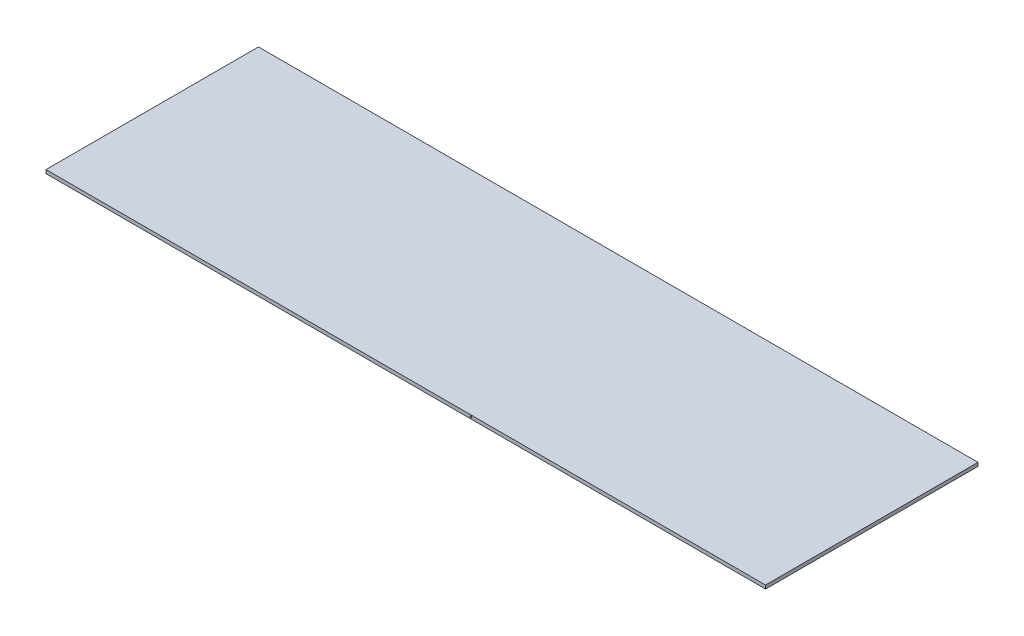
SolidWorks part; units mm, degrees
material "Maple"
ref_plane "Front Plane" through (0, 0, 0) normal (0, 0, 1) x (1, 0, 0)
ref_plane "Top Plane" through (0, 0, 0) normal (0, 1, 0) x (1, 0, 0)
ref_plane "Right Plane" through (0, 0, 0) normal (1, 0, 0) x (0, 0, -1)
sketch "Sketch1" plane through (0, 0, 0) normal (0, 1, 0) x (1, 0, 0)
  line L1 (0, 0) -> (1016, 0)
  line L2 (0, 0) -> (0, 300)
  line L3 (0, 300) -> (1016, 300)
  line L4 (1016, 0) -> (1016, 300)
  dimension "D1" = 1016
  dimension "D2" = 300
extrude "Boss-Extrude1" add sketch "Sketch1" along normal blind 5
sketch "Sketch2" plane through (0, 0, 0) normal (0, 0, 1) x (1, 0, 0)
  circle A0 centre (600, 2.5763) radius 1.25
  dimension "D1" = 2.5
  dimension "D2" = 600
extrude "Cut-Extrude1" cut sketch "Sketch2" against normal through all
